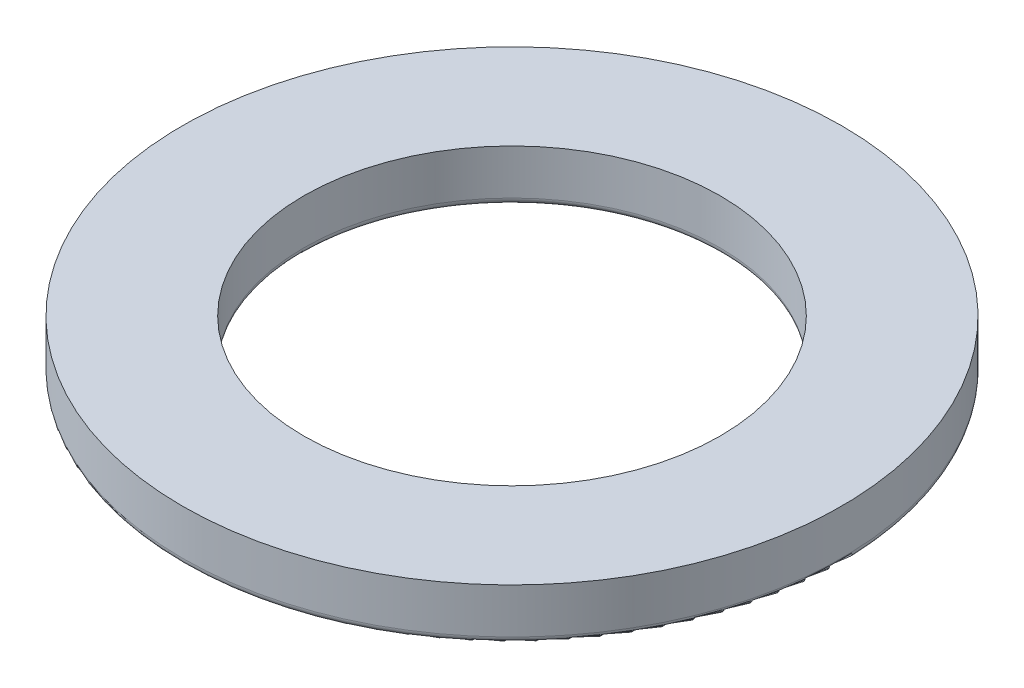
SolidWorks part; units mm, degrees
ref_plane "Front Plane" through (0, 0, 0) normal (0, 0, 1) x (1, 0, 0)
ref_plane "Top Plane" through (0, 0, 0) normal (0, 1, 0) x (1, 0, 0)
ref_plane "Right Plane" through (0, 0, 0) normal (1, 0, 0) x (0, 0, -1)
sketch "Sketch1" plane through (0, 0, 0) normal (0, 1, 0) x (1, 0, 0)
  circle A0 centre (0, 0) radius 9.5
  circle A1 centre (0, 0) radius 6
  dimension "D1" = 19
  dimension "D2" = 12
extrude "Boss-Extrude1" add sketch "Sketch1" along normal blind 1.5
fillet "Fillet1" radius 0.2 2 edges at (0, 0, 6) (0, 0, 9.5)
